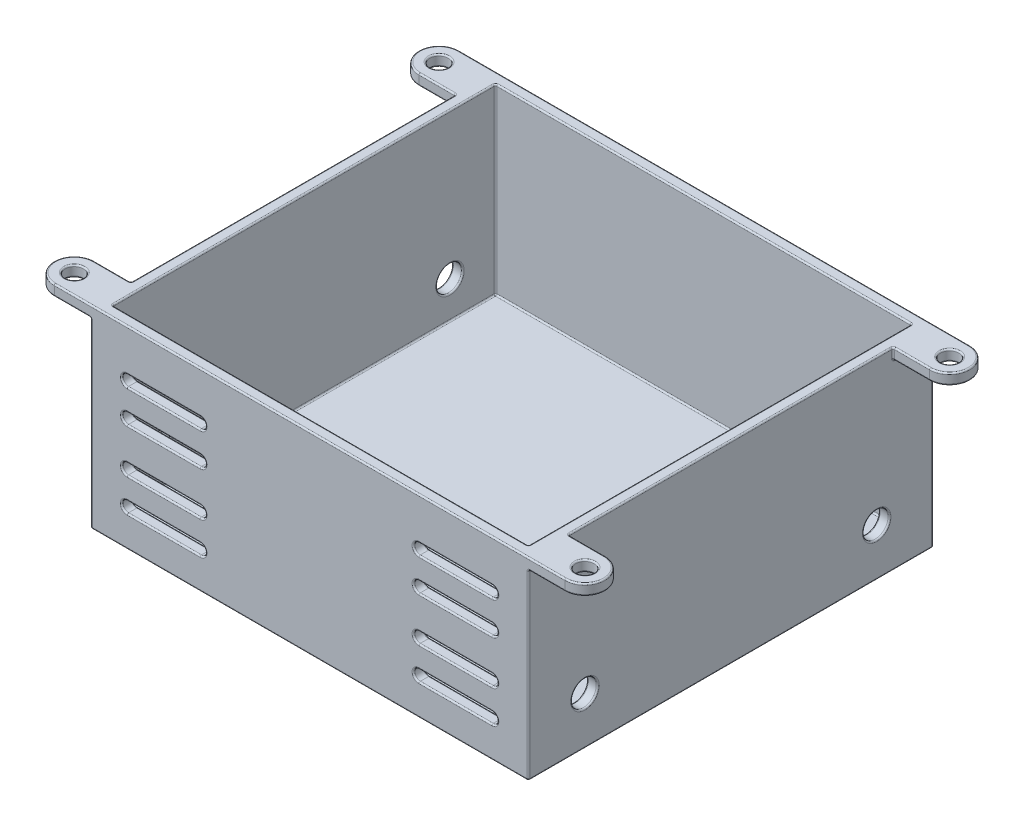
SolidWorks part; units mm, degrees
ref_plane "Front Plane" through (0, 0, 0) normal (0, 0, 1) x (1, 0, 0)
ref_plane "Top Plane" through (0, 0, 0) normal (0, 1, 0) x (1, 0, 0)
ref_plane "Right Plane" through (0, 0, 0) normal (1, 0, 0) x (0, 0, -1)
sketch "Sketch2" plane through (0, 0, 0) normal (0, 1, 0) x (1, 0, 0)
  line L0 (-35, 27.75) -> (35, 27.75) construction
  line L1 (-35, 25) -> (35, 25) construction
  line L2 (-35, 25) -> (-35, -25) construction
  line L3 (-35, -25) -> (35, -25) construction
  line L4 (35, 25) -> (35, -25) construction
  line L5 (-35, 25) -> (35, -25) construction
  line L6 (-35, -25) -> (35, 25) construction
  line L7 (37.75, 25) -> (37.75, -25) construction
  line L8 (35, -27.75) -> (-35, -27.75) construction
  line L9 (-37.75, 25) -> (-37.75, -25) construction
  line L14 (-35, 22.25) -> (-30, 22.25)
  line L15 (35, 22.25) -> (30, 22.25)
  line L16 (-35, -22.25) -> (-30, -22.25)
  line L17 (35, -22.25) -> (30, -22.25)
  line L19 (-30, 27.75) -> (-30, -27.75)
  line L20 (-30, -27.75) -> (30, -27.75)
  line L21 (30, -27.75) -> (30, 27.75)
  line L22 (30, 27.75) -> (-30, 27.75)
  circle A0 centre (-35, 25) radius 1.25
  circle A1 centre (35, 25) radius 1.25
  circle A2 centre (35, -25) radius 1.25
  circle A3 centre (-35, -25) radius 1.25
  circle A4 centre (-35, 25) radius 2.75
  circle A5 centre (35, 25) radius 2.75
  circle A6 centre (35, -25) radius 2.75
  circle A7 centre (-35, -25) radius 2.75
  point P0 (0, 0)
  point P28 (0, 27.75)
  dimension "D3" = 2.5
  dimension "D1" = 70
  dimension "D2" = 50
  dimension "D5" = 60
  dimension "D4" = 1.5
sketch "Sketch8" plane through (0, 0, 0) normal (0, 1, 0) x (1, 0, 0)
  line L0 (-30, -27.75) -> (30, -27.75) construction
  line L1 (30, -27.75) -> (30, 27.75) construction
  line L2 (30, 27.75) -> (-30, 27.75) construction
  line L3 (-30, 27.75) -> (-30, -27.75) construction
  line L4 (-30, -27.75) -> (30, -27.75)
  line L5 (30, -27.75) -> (30, 27.75)
  line L6 (30, 27.75) -> (-30, 27.75)
  line L7 (-30, 27.75) -> (-30, -27.75)
  line L8 (28.5, 26.25) -> (-28.5, 26.25)
  line L9 (-28.5, 26.25) -> (-28.5, -26.25)
  line L10 (-28.5, -26.25) -> (28.5, -26.25)
  line L11 (28.5, -26.25) -> (28.5, 26.25)
  dimension "D1" = 1.5
extrude "Boss-Extrude4" add sketch "Sketch8" against normal blind 25
sketch "Sketch9" plane through (0, -25, 0) normal (0, -1, 0) x (1, 0, 0)
  line L4 (-30, 27.75) -> (-30, -27.75)
  line L5 (-30, -27.75) -> (30, -27.75)
  line L6 (30, -27.75) -> (30, 27.75)
  line L7 (30, 27.75) -> (-30, 27.75)
  line L8 (-30, 27.75) -> (-30, -27.75)
  line L9 (-30, -27.75) -> (30, -27.75)
  line L10 (30, -27.75) -> (30, 27.75)
  line L11 (30, 27.75) -> (-30, 27.75)
  dimension "D1" = 0
extrude "Boss-Extrude5" add sketch "Sketch9" along normal blind 1.5
sketch "Sketch10" plane through (0, 0, 0) normal (0, 1, 0) x (1, 0, 0)
  line L0 (35, 22.25) -> (30, 22.25) construction
  line L1 (35, -22.25) -> (30, -22.25) construction
  line L2 (-35, -22.25) -> (-30, -22.25) construction
  line L3 (-35, 22.25) -> (-30, 22.25) construction
  line L4 (-30, 27.75) -> (-30, -27.75)
  line L5 (-30, -27.75) -> (30, -27.75)
  line L6 (30, -27.75) -> (30, 27.75)
  line L7 (30, 27.75) -> (-30, 27.75)
  line L8 (-30, -22.25) -> (-30, -27.75)
  line L10 (30, -27.75) -> (30, -22.25)
  line L12 (35, 22.25) -> (30, 22.25)
  line L13 (35, -22.25) -> (30, -22.25)
  line L14 (-35, -22.25) -> (-30, -22.25)
  line L15 (-35, 22.25) -> (-30, 22.25)
  line L16 (35, 27.75) -> (30, 27.75)
  line L17 (-35, 27.75) -> (-30, 27.75)
  line L19 (-35, -27.75) -> (-30, -27.75)
  line L20 (30, 27.75) -> (30, 22.25)
  line L21 (-30, 27.75) -> (-30, 22.25)
  line L22 (35, -27.75) -> (30, -27.75)
  arc A0 (-35, -27.75) -> (-35, -22.25) centre (-35, -25) cw
  arc A1 (35, -27.75) -> (35, -22.25) centre (35, -25) ccw
  arc A3 (35, 22.25) -> (35, 27.75) centre (35, 25) ccw
  arc A5 (-35, 22.25) -> (-35, 27.75) centre (-35, 25) cw
  circle A7 centre (-35, -25) radius 1.25
  circle A8 centre (-35, -25) radius 1.25
  circle A9 centre (35, -25) radius 1.25
  circle A10 centre (35, -25) radius 1.25
  circle A11 centre (35, 25) radius 1.25
  circle A12 centre (35, 25) radius 1.25
  circle A13 centre (-35, 25) radius 1.25
  circle A14 centre (-35, 25) radius 1.25
  dimension "D4" = 0
  dimension "D5" = 0
  dimension "D6" = 0
  dimension "D7" = 0
  dimension "D9" = 0
extrude "Boss-Extrude6" add sketch "Sketch10" against normal blind 1.5
sketch "Sketch13" plane through (0, 0, 0) normal (0, 0, 1) x (1, 0, 0)
  line L0 (30, -14) -> (-30, -14) construction
  line L1 (30, -26.5) -> (30, -1.5) construction
  line L2 (-30, -26.5) -> (-30, -1.5) construction
  line L3 (-25, -6.5) -> (-15, -6.5) construction
  line L4 (-25, -5.75) -> (-15, -5.75)
  line L5 (-25, -7.25) -> (-15, -7.25)
  line L6 (-25, -11) -> (-15, -11) construction
  line L7 (-25, -10.25) -> (-15, -10.25)
  line L8 (-25, -11.75) -> (-15, -11.75)
  line L9 (0, -14) -> (0, -21.2543) construction
  line L10 (-25, -21.5) -> (-15, -21.5) construction
  line L11 (-25, -22.25) -> (-15, -22.25)
  line L12 (-25, -20.75) -> (-15, -20.75)
  line L13 (-25, -17) -> (-15, -17) construction
  line L14 (-25, -17.75) -> (-15, -17.75)
  line L15 (-25, -16.25) -> (-15, -16.25)
  line L16 (25, -6.5) -> (15, -6.5) construction
  line L17 (25, -5.75) -> (15, -5.75)
  line L18 (25, -7.25) -> (15, -7.25)
  line L19 (25, -11) -> (15, -11) construction
  line L20 (25, -10.25) -> (15, -10.25)
  line L21 (25, -11.75) -> (15, -11.75)
  line L22 (25, -21.5) -> (15, -21.5) construction
  line L23 (25, -22.25) -> (15, -22.25)
  line L24 (25, -20.75) -> (15, -20.75)
  line L25 (25, -17) -> (15, -17) construction
  line L26 (25, -17.75) -> (15, -17.75)
  line L27 (25, -16.25) -> (15, -16.25)
  arc A0 (-25, -5.75) -> (-25, -7.25) centre (-25, -6.5) ccw
  arc A1 (-15, -7.25) -> (-15, -5.75) centre (-15, -6.5) ccw
  arc A2 (-25, -10.25) -> (-25, -11.75) centre (-25, -11) ccw
  arc A3 (-15, -11.75) -> (-15, -10.25) centre (-15, -11) ccw
  arc A4 (-25, -22.25) -> (-25, -20.75) centre (-25, -21.5) cw
  arc A5 (-15, -20.75) -> (-15, -22.25) centre (-15, -21.5) cw
  arc A6 (-25, -17.75) -> (-25, -16.25) centre (-25, -17) cw
  arc A7 (-15, -16.25) -> (-15, -17.75) centre (-15, -17) cw
  arc A8 (25, -5.75) -> (25, -7.25) centre (25, -6.5) cw
  arc A9 (15, -7.25) -> (15, -5.75) centre (15, -6.5) cw
  arc A10 (25, -10.25) -> (25, -11.75) centre (25, -11) cw
  arc A11 (15, -11.75) -> (15, -10.25) centre (15, -11) cw
  arc A12 (25, -22.25) -> (25, -20.75) centre (25, -21.5) ccw
  arc A13 (15, -20.75) -> (15, -22.25) centre (15, -21.5) ccw
  arc A14 (25, -17.75) -> (25, -16.25) centre (25, -17) ccw
  arc A15 (15, -16.25) -> (15, -17.75) centre (15, -17) ccw
  point P8 (-20, -6.5)
  point P16 (-20, -11)
  point P25 (-20, -21.5)
  point P32 (-20, -17)
  point P39 (20, -6.5)
  point P46 (20, -11)
  point P53 (20, -21.5)
  point P60 (20, -17)
  dimension "D1" = 10
  dimension "D2" = 1.5
  dimension "D3" = 20
  dimension "D4" = 7.5
  dimension "D5" = 4.5
extrude "Cut-Extrude1" cut sketch "Sketch13" along normal up to surface and the other way up to surface up to face at (0, -7.375, 27.75) other way up to face at (0, -12.5, -26.25)
sketch "Sketch14" plane through (0, 0, 0) normal (1, 0, 0) x (0, 0, -1)
  line L0 (0, 0) -> (0, -20) construction
  line L1 (0, -20) -> (-20, -20) construction
  circle A0 centre (-20, -20) radius 1.75
  circle A1 centre (20, -20) radius 1.75
  dimension "D1" = 3.5
  dimension "D2" = 20
  dimension "D3" = 20
extrude "Cut-Extrude2" cut sketch "Sketch14" along normal up to surface and the other way up to surface up to face at (30, -7.375, 0) other way up to face at (-30, -7.375, 0)
fillet "Fillet1" radius 0.2 132 edges at (-30, -20, -18.25) (30, -20, -21.75) (-30, -20, 21.75) (30, -20, 18.25) (-28.5, -20, -18.25) (28.5, -20, -21.75) (-28.5, -20, 21.75) (28.5, -20, 18.25) (20, -17.75, 27.75) (25.75, -17, 27.75) (20, -16.25, 27.75) (14.25, -17, 27.75) (20, -22.25, 27.75) (25.75, -21.5, 27.75) (20, -20.75, 27.75) (14.25, -21.5, 27.75) (20, -11.75, 27.75) (25.75, -11, 27.75) (20, -10.25, 27.75) (14.25, -11, 27.75) (20, -7.25, 27.75) (25.75, -6.5, 27.75) (20, -5.75, 27.75) (14.25, -6.5, 27.75) (-20, -16.25, 27.75) (-25.75, -17, 27.75) (-20, -17.75, 27.75) (-14.25, -17, 27.75) (-20, -20.75, 27.75) (-25.75, -21.5, 27.75) (-20, -22.25, 27.75) (-14.25, -21.5, 27.75) (-20, -10.25, 27.75) (-25.75, -11, 27.75) (-20, -11.75, 27.75) (-14.25, -11, 27.75) (-20, -5.75, 27.75) (-25.75, -6.5, 27.75) (-20, -7.25, 27.75) (-14.25, -6.5, 27.75) (-20, -5.75, 26.25) (-14.25, -6.5, 26.25) (-20, -7.25, 26.25) (-25.75, -6.5, 26.25) (20, -11.75, 26.25) (14.25, -11, 26.25) (20, -10.25, 26.25) (25.75, -11, 26.25) (20, -22.25, 26.25) (14.25, -21.5, 26.25) (20, -20.75, 26.25) (25.75, -21.5, 26.25) (20, -17.75, 26.25) (14.25, -17, 26.25) (20, -16.25, 26.25) (25.75, -17, 26.25) (-20, -10.25, 26.25) (-14.25, -11, 26.25) (-20, -11.75, 26.25) (-25.75, -11, 26.25) (-20, -20.75, 26.25) (-14.25, -21.5, 26.25) (-20, -22.25, 26.25) (-25.75, -21.5, 26.25) (-20, -16.25, 26.25) (-14.25, -17, 26.25) (-20, -17.75, 26.25) (-25.75, -17, 26.25) (20, -7.25, 26.25) (14.25, -6.5, 26.25) (20, -5.75, 26.25) (25.75, -6.5, 26.25) (35, 0, 26.25) (35, -1.5, 26.25) (37.75, 0, 25) (37.75, -1.5, 25) (32.5, 0, 22.25) (32.5, -1.5, 22.25) (32.5, -1.5, 27.75) (30, -1.5, 25) (30, -0.75, 22.25) (35, 0, -23.75) (35, -1.5, -23.75) (37.75, 0, -25) (37.75, -1.5, -25) (32.5, 0, -22.25) (32.5, -1.5, -22.25) (32.5, -1.5, -27.75) (30, -1.5, -25) (30, -0.75, -22.25) (-35, 0, 26.25) (-35, -1.5, 26.25) (-32.5, 0, 22.25) (-32.5, -1.5, 22.25) (-37.75, 0, 25) (-37.75, -1.5, 25) (-32.5, -1.5, 27.75) (-30, -1.5, 25) (-30, -0.75, 22.25) (-35, 0, -23.75) (-35, -1.5, -23.75) (-37.75, 0, -25) (-37.75, -1.5, -25) (-32.5, 0, -22.25) (-32.5, -1.5, -22.25) (-30, -1.5, -25) (-32.5, -1.5, -27.75) (-30, -0.75, -22.25) (0, -26.5, 27.75) (-30, -26.5, 0) (0, -26.5, -27.75) (30, -26.5, 0) (28.5, 0, 0) (0, 0, -26.25) (-28.5, 0, 0) (0, 0, 26.25) (28.5, -25, 0) (0, -25, -26.25) (-28.5, -25, 0) (0, -25, 26.25) (28.5, -12.5, -26.25) (-28.5, -12.5, -26.25) (-28.5, -12.5, 26.25) (28.5, -12.5, 26.25) (-30, 0, 0) (0, 0, 27.75) (30, 0, 0) (0, 0, -27.75) (30, -14, 27.75) (30, -14, -27.75) (-30, -14, -27.75) (-30, -14, 27.75)
